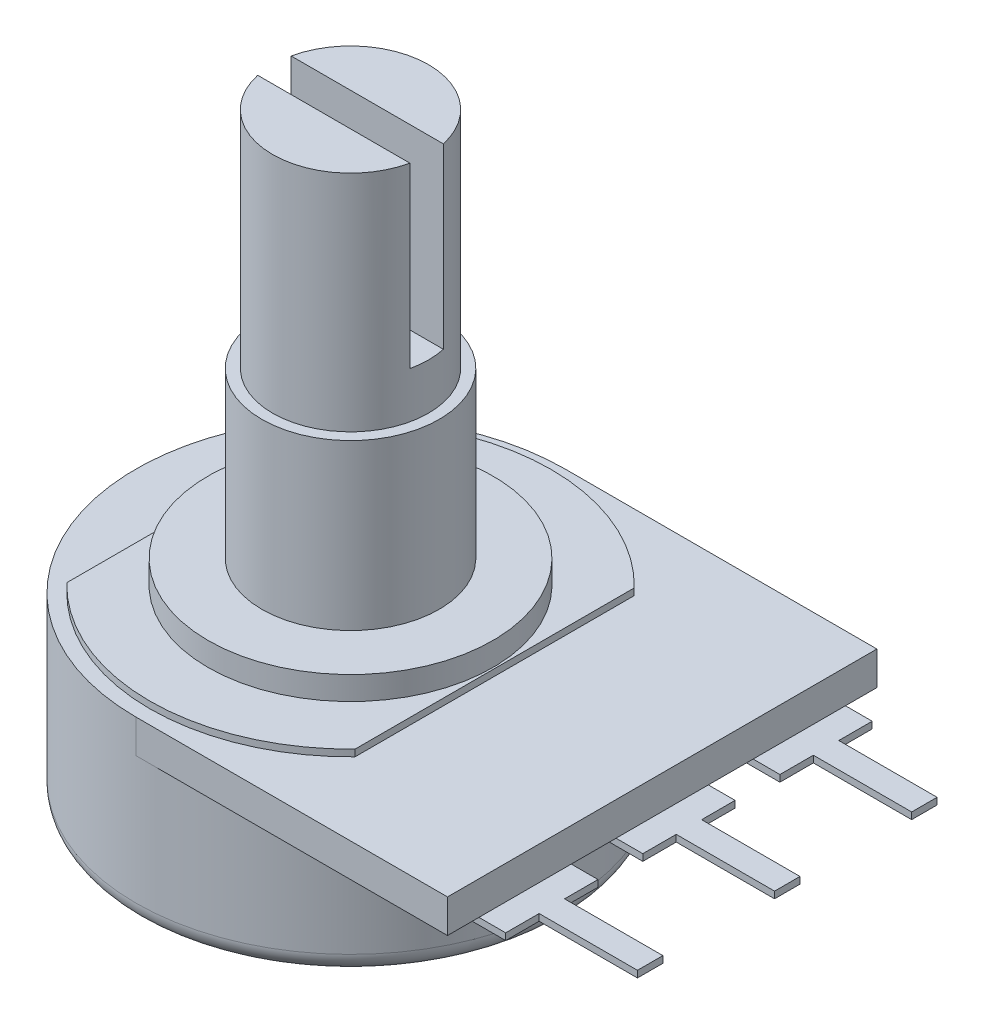
SolidWorks part; units mm, degrees
ref_plane "Front Plane" through (0, 0, 0) normal (0, 0, 1) x (1, 0, 0)
ref_plane "Top Plane" through (0, 0, 0) normal (0, 1, 0) x (1, 0, 0)
ref_plane "Right Plane" through (0, 0, 0) normal (1, 0, 0) x (0, 0, -1)
sketch "Sketch1" plane through (0, 0, 0) normal (0, 1, 0) x (1, 0, 0)
  circle A0 centre (0, 0) radius 8.1534
  dimension "D1" = 16.3068
extrude "Boss-Extrude1" add sketch "Sketch1" along normal blind 5.6134
sketch "Sketch2" plane through (0, 5.6134, 0) normal (0, 1, 0) x (1, 0, 0)
  line L0 (0, 8.1534) -> (11.8364, 8.1534)
  line L1 (11.8364, 8.1534) -> (11.8364, -8.1534)
  line L2 (11.8364, -8.1534) -> (0, -8.1534)
  arc A0 (0, -8.1534) -> (0, 8.1534) centre (0, 0) cw
  circle A1 centre (0, 0) radius 8.1534 construction
  dimension "D1" = 11.8364
extrude "Boss-Extrude2" add sketch "Sketch2" along normal blind 1.27
sketch "Sketch3" plane through (0, 6.8834, 0) normal (0, 1, 0) x (1, 0, 0)
  line L0 (-5.4737, 5.3012) -> (-5.4737, -5.3012)
  line L1 (5.4737, 5.3012) -> (5.4737, -5.3012)
  arc A0 (-5.4737, -5.3012) -> (5.4737, -5.3012) centre (0, 0) ccw
  arc A1 (5.4737, 5.3012) -> (-5.4737, 5.3012) centre (0, 0) ccw
  dimension "D1" = 15.24
  dimension "D2" = 10.9474
extrude "Boss-Extrude3" add sketch "Sketch3" along normal blind 0.254
sketch "Sketch4" plane through (0, 7.1374, 0) normal (0, 1, 0) x (1, 0, 0)
  circle A0 centre (0, 0) radius 5.4102
  dimension "D1" = 10.8204
extrude "Boss-Extrude4" add sketch "Sketch4" along normal blind 0.889
sketch "Sketch5" plane through (0, 8.0264, 0) normal (0, 1, 0) x (1, 0, 0)
  circle A0 centre (0, 0) radius 3.3655
  dimension "D1" = 6.731
extrude "Boss-Extrude5" add sketch "Sketch5" along normal blind 6.2484
sketch "Sketch6" plane through (0, 14.2748, 0) normal (0, 1, 0) x (1, 0, 0)
  circle A0 centre (0, 0) radius 2.9591
  dimension "D1" = 5.9182
extrude "Boss-Extrude6" add sketch "Sketch6" along normal blind 8.509
sketch "Sketch7" plane through (0, 22.7838, 0) normal (0, 1, 0) x (1, 0, 0)
  line L1 (4.3863, -0.635) -> (-4.3863, -0.635)
  line L2 (4.3863, -0.635) -> (4.3863, 0.635)
  line L3 (4.3863, 0.635) -> (-4.3863, 0.635)
  line L4 (-4.3863, -0.635) -> (-4.3863, 0.635)
  line L5 (4.3863, -0.635) -> (-4.3863, 0.635) construction
  line L6 (4.3863, 0.635) -> (-4.3863, -0.635) construction
  point P0 (0, 0)
  dimension "D1" = 1.27
extrude "Cut-Extrude1" cut sketch "Sketch7" against normal blind 6.7564
sketch "Sketch8" plane through (0, 5.6134, 0) normal (0, -1, 0) x (1, 0, 0)
  line L0 (11.8364, 8.1534) -> (11.8364, -8.1534) construction
  line L1 (8.3507, 1.7526) -> (12.8524, 1.7526)
  line L2 (8.3507, 1.7526) -> (8.3507, -1.7526)
  line L3 (8.3507, -1.7526) -> (12.8524, -1.7526)
  line L4 (12.8524, 1.7526) -> (12.8524, 0.4826)
  line L5 (12.8524, -0.4826) -> (12.8524, -1.7526)
  line L6 (12.8524, -0.4826) -> (16.5862, -0.4826)
  line L8 (12.8524, 0.4826) -> (16.5862, 0.4826)
  line L9 (16.5862, -0.4826) -> (16.5862, 0.4826)
  point P12 (16.5862, 0)
  dimension "D1" = 3.5052
  dimension "D2" = 1.016
  dimension "D3" = 0.9652
  dimension "D4" = 3.7338
extrude "Boss-Extrude7" add sketch "Sketch8" along normal blind 0.254
pattern_linear "LPattern1" count 2 spacing 5.207 along (0, 0, -1) of "Boss-Extrude7"
pattern_linear "LPattern2" count 2 spacing 5.207 along (0, 0, 1) of "Boss-Extrude7"
fillet "Fillet1" radius 0.762 1 edges at (0, 0, 8.1534)
